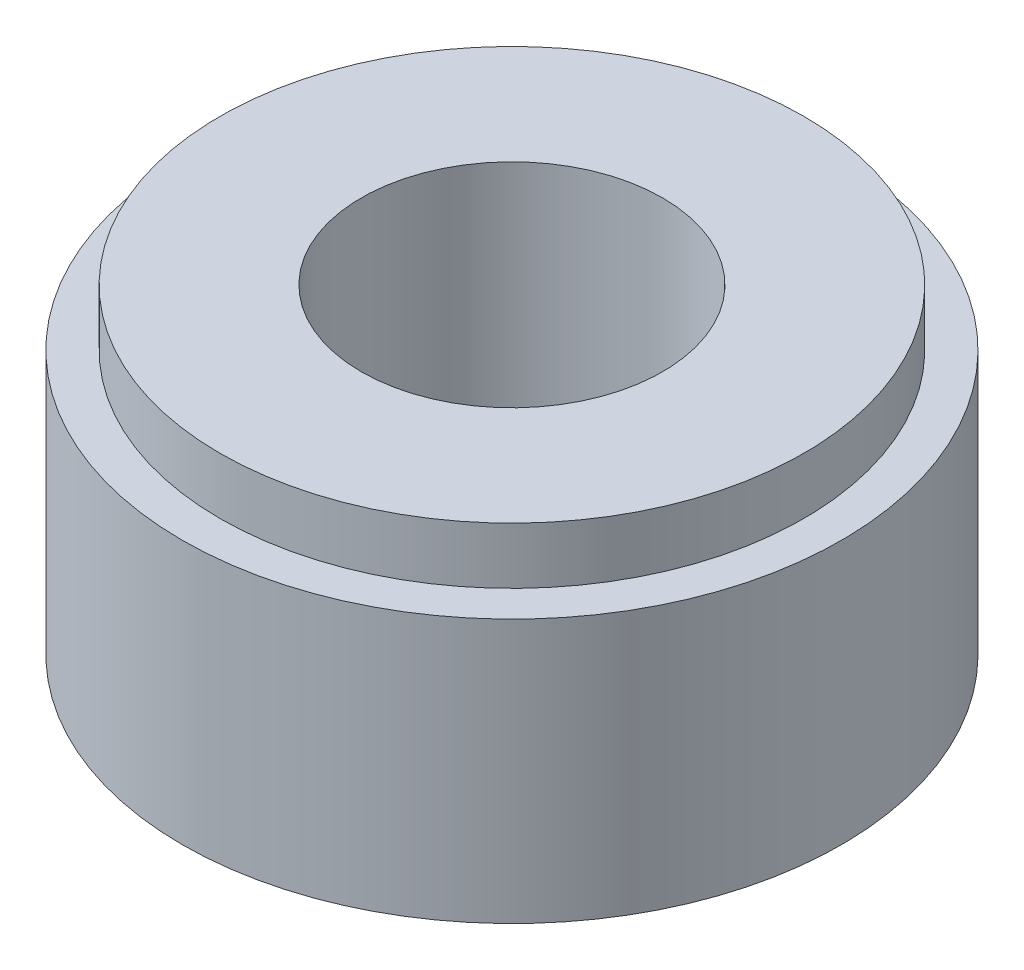
SolidWorks part; units mm, degrees
ref_plane "Front Plane" through (0, 0, 0) normal (0, 0, 1) x (1, 0, 0)
ref_plane "Top Plane" through (0, 0, 0) normal (0, 1, 0) x (1, 0, 0)
ref_plane "Right Plane" through (0, 0, 0) normal (1, 0, 0) x (0, 0, -1)
sketch "Sketch1" plane through (0, 0, 0) normal (0, 1, 0) x (1, 0, 0)
  circle A0 centre (0, 0) radius 17.5
extrude "Boss-Extrude1" add sketch "Sketch1" along normal blind 14
sketch "Sketch2" plane through (0, 14, 0) normal (0, 1, 0) x (1, 0, 0)
  circle A0 centre (0, 0) radius 15.5
extrude "Boss-Extrude2" add sketch "Sketch2" along normal blind 3
sketch "Sketch3" plane through (0, 17, 0) normal (0, 1, 0) x (1, 0, 0)
  circle A0 centre (0, 0) radius 8
extrude "Cut-Extrude1" cut sketch "Sketch3" against normal through all
